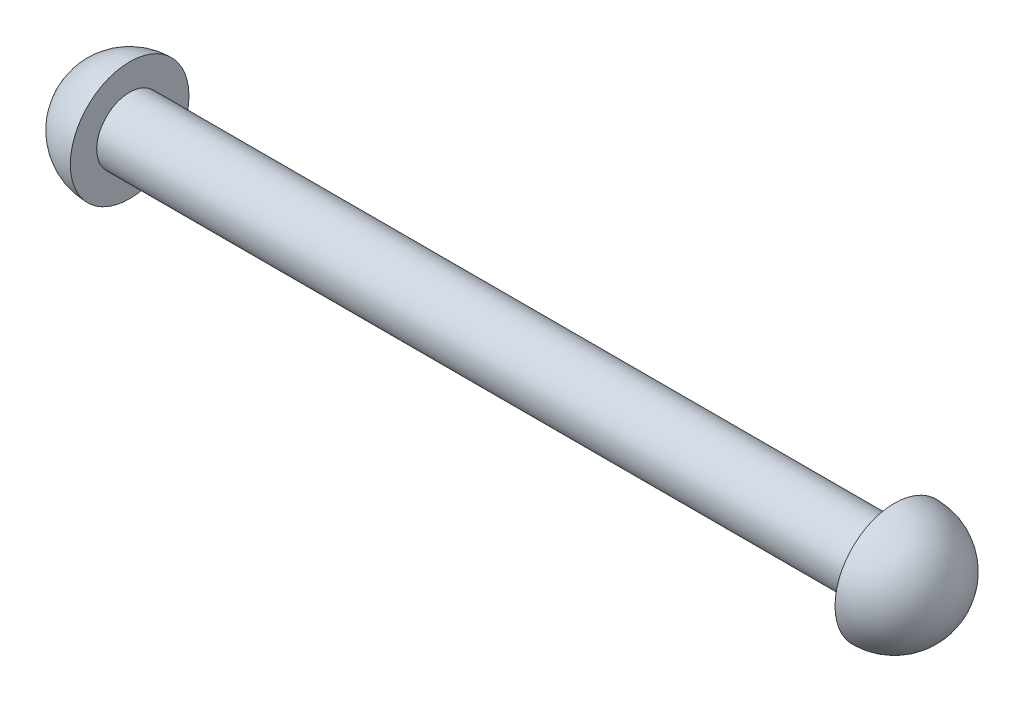
SolidWorks part; units mm, degrees
material "AISI 1020"
ref_plane "Front Plane" through (0, 0, 0) normal (0, 0, 1) x (1, 0, 0)
ref_plane "Top Plane" through (0, 0, 0) normal (0, 1, 0) x (1, 0, 0)
ref_plane "Right Plane" through (0, 0, 0) normal (1, 0, 0) x (0, 0, -1)
sketch "Sketch1" plane through (0, 0, 0) normal (0, 0, 1) x (1, 0, 0)
  line L0 (0, 0) -> (63.2872, 0) construction
  line L1 (5.715, 5.715) -> (5.715, 3.175)
  line L2 (5.715, 3.175) -> (79.375, 3.175)
  line L3 (0, 0) -> (0, 12.1658) construction
  line L4 (42.545, 3.175) -> (42.545, 0) construction
  line L5 (79.375, 5.715) -> (79.375, 3.175)
  line L6 (0, 0) -> (85.09, 0)
  arc A0 (0, 0) -> (5.715, 5.715) centre (5.715, 0) cw
  arc A1 (85.09, 0) -> (79.375, 5.715) centre (79.375, 0) ccw
  dimension "D2" = 5.715
  dimension "D1" = 36.83
  dimension "D3" = 6.35
  dimension "D4" = 11.43
revolve "Revolve1" add sketch "Sketch1" angle 360 about L6
